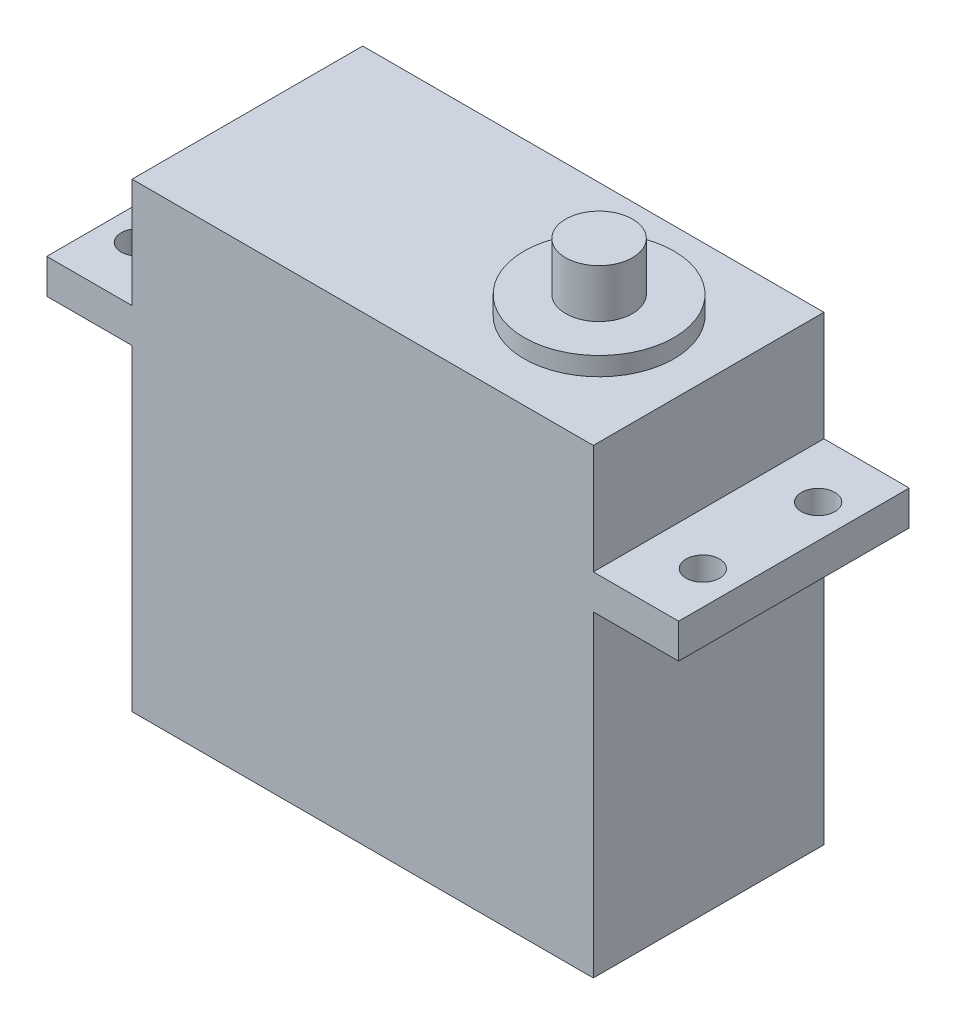
SolidWorks part; units mm, degrees
ref_plane "Front Plane" through (0, 0, 0) normal (0, 0, 1) x (1, 0, 0)
ref_plane "Top Plane" through (0, 0, 0) normal (0, 1, 0) x (1, 0, 0)
ref_plane "Right Plane" through (0, 0, 0) normal (1, 0, 0) x (0, 0, -1)
sketch "Sketch1" plane through (0, 0, 0) normal (0, 1, 0) x (1, 0, 0)
  line L1 (-20, -10) -> (20, -10)
  line L2 (-20, -10) -> (-20, 10)
  line L3 (-20, 10) -> (20, 10)
  line L4 (20, -10) -> (20, 10)
  line L5 (-20, -10) -> (20, 10) construction
  line L6 (-20, 10) -> (20, -10) construction
  point P0 (0, 0)
  dimension "D1" = 20
  dimension "D2" = 40
extrude "Boss-Extrude1" add sketch "Sketch1" along normal blind 40
sketch "Sketch2" plane through (20, 0, 0) normal (1, 0, 0) x (0, 0, -1)
  line L0 (-10, 40) -> (-10, 0) construction
  line L1 (-10, 30.5) -> (10, 30.5)
  line L2 (-10, 30.5) -> (-10, 27.5)
  line L3 (-10, 27.5) -> (10, 27.5)
  line L4 (10, 30.5) -> (10, 27.5)
  line L5 (10, 40) -> (10, 0) construction
  line L6 (-10, 0) -> (10, 0) construction
  dimension "D1" = 30.5
  dimension "D3" = 27.5
extrude "Boss-Extrude2" add sketch "Sketch2" along normal blind 7.4
mirror "Mirror1" about plane through (0, 0, 0) normal (1, 0, 0) of "Boss-Extrude2"
sketch "Sketch3" plane through (0, 40, 0) normal (0, 1, 0) x (1, 0, 0)
  line L0 (7.6, 0) -> (20, 0) construction
  line L2 (20, 10) -> (20, -10) construction
  circle A0 centre (10.5, 0) radius 2.9
  dimension "D1" = 5.8
  dimension "D2" = 12.4
  dimension "D3" = 9.5
extrude "Boss-Extrude3" add sketch "Sketch3" along normal blind 5.8
sketch "Sketch5" plane through (0, 40, 0) normal (0, 1, 0) x (1, 0, 0)
  circle A0 centre (10.5, 0) radius 6.5
  dimension "D1" = 13
extrude "Boss-Extrude4" add sketch "Sketch5" along normal blind 1.6
hole_wizard "M2.5 Clearance Slot1" positions "Sketch6" profile "Sketch7" size "M2.5" standard "ANSI Metric" slot yes
sketch "Sketch6" plane through (-162.1143, 30.5, -5.4319) normal (0, 1, 0) x (0.4127, 0, 0.9109)
  point P0 (57.1895, 125.1689)
  point P2 (66.2981, 121.0417)
  point P4 (77.4128, 169.8009)
  point P6 (86.5214, 165.6737)
sketch "Sketch7" plane through (-24.5, 30.5, -5) normal (1, 0, 0) x (0, 0, 1)
  line L0 (0, 0) -> (0, 9.8702)
  line L1 (0, 9.8702) -> (1.45, 8.999)
  line L2 (1.45, 8.999) -> (1.45, 0)
  line L3 (1.45, 0) -> (0, 0)
  line L4 (0, 9.8702) -> (-1.45, 8.999) construction
  line L5 (0, -6.35) -> (0, 107.95) construction
  dimension "Hole Dia." = 2.9
  dimension "Hole Depth" = 8.999
  dimension "Drill Angle" = 118
